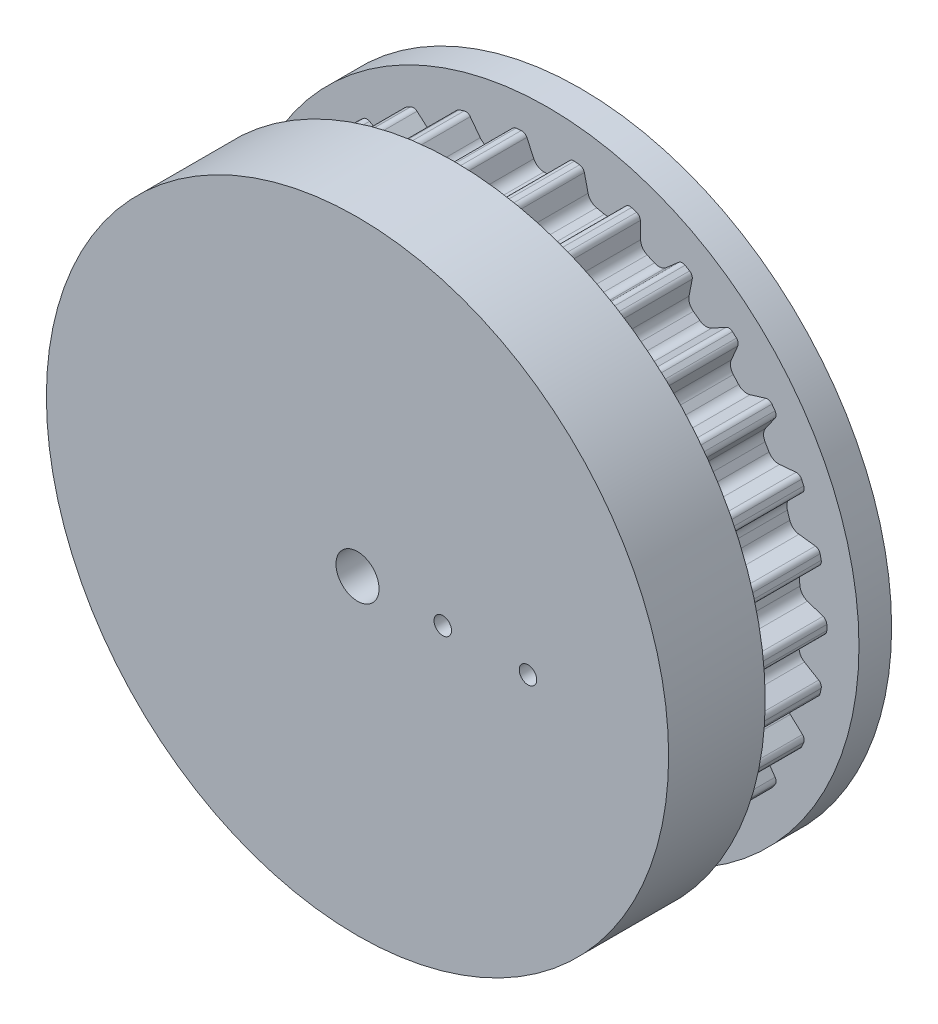
SolidWorks part; units mm, degrees
ref_plane "Front Plane" through (0, 0, 0) normal (0, 0, 1) x (1, 0, 0)
ref_plane "Top Plane" through (0, 0, 0) normal (0, 1, 0) x (1, 0, 0)
ref_plane "Right Plane" through (0, 0, 0) normal (1, 0, 0) x (0, 0, -1)
sketch "Sketch1" plane through (0, 0, 0) normal (0, 0, 1) x (1, 0, 0)
  line L0 (-5.3109, 65.2292) -> (-2.5867, 59.3872)
  line L1 (-2.5867, 59.3872) -> (2.5867, 59.3872)
  line L2 (2.5867, 59.3872) -> (5.3109, 65.2292)
  line L3 (-5.3109, 65.2292) -> (5.3109, 65.2292)
  line L4 (0, 0) -> (0, 59.3872) construction
  line L5 (0, 59.3872) -> (0, 66.84) construction
  circle A0 centre (0, 0) radius 66.84 construction
  circle A1 centre (0, 0) radius 65.445 construction
  circle A2 centre (0, 0) radius 65.445 construction
  circle A3 centre (0, 0) radius 73
  circle A4 centre (0, 0) radius 55.5
  circle A5 centre (0, 0) radius 20 construction
  point P6 (0, 65.2292)
  point P11 (0, 66.84)
  point P13 (0, 65.445)
  point P14 (0, 65.445)
  point P21 (13.5619, 63.8037)
  point P22 (26.5311, 59.5898)
  point P23 (38.3407, 52.7715)
  point P24 (48.4747, 43.6468)
  point P25 (56.4901, 32.6146)
  point P26 (62.0366, 20.1569)
  point P27 (64.8718, 6.8183)
  point P28 (64.8718, -6.8183)
  point P29 (62.0366, -20.1569)
  point P30 (56.4901, -32.6146)
  point P31 (48.4747, -43.6468)
  point P32 (38.3407, -52.7715)
  point P33 (26.5311, -59.5898)
  point P34 (13.5619, -63.8037)
  point P35 (0, -65.2292)
  point P36 (-13.5619, -63.8037)
  point P37 (-26.5311, -59.5898)
  point P38 (-38.3407, -52.7715)
  point P39 (-48.4747, -43.6468)
  point P40 (-56.4901, -32.6146)
  point P41 (-62.0366, -20.1569)
  point P42 (-64.8718, -6.8183)
  point P43 (-64.8718, 6.8183)
  point P44 (-62.0366, 20.1569)
  point P45 (-56.4901, 32.6146)
  point P46 (-48.4747, 43.6468)
  point P47 (-38.3407, 52.7715)
  point P48 (-26.5311, 59.5898)
  point P49 (-13.5619, 63.8037)
  point P52 (0, 0)
  dimension "Pitch Diameter" = 133.68
  dimension "Diameter" = 130.89
  dimension "OD" = 146
  dimension "Hub Diameter" = 111
  dimension "For Shaft Diameter" = 40
  dimension "b" = 50
  dimension "Tooth Width" = 10.6218
  dimension "ht" = 5.842
  dimension "Number of Teeth" = 30
sketch "Sketch2" plane through (0, 0, 0) normal (1, 0, 0) x (0, 0, -1)
  line L0 (29.335, 0) -> (-29.335, 0) construction
  line L3 (29.335, 20) -> (-29.335, 20)
  line L4 (-29.335, 20) -> (-29.335, 55.5)
  line L5 (29.335, 20) -> (29.335, 73)
  line L6 (29.335, 73) -> (21.675, 73)
  line L7 (21.675, 73) -> (21.675, 65.2292)
  line L8 (21.675, 65.2292) -> (-15.325, 65.2292)
  line L9 (-15.325, 65.2292) -> (-15.325, 73)
  line L10 (-15.325, 73) -> (-22.985, 73)
  line L11 (-29.335, 55.5) -> (-22.985, 55.5)
  line L12 (-22.985, 73) -> (-22.985, 55.5)
  line L13 (-22.985, 55.5) -> (0, 55.5) construction
  point P0 (0, 20)
  point P3 (0, 20)
  point P4 (0, 0)
  point P6 (0, 73)
  point P16 (21.675, 69.1146)
  dimension "Overall Width" = 58.67
  dimension "For Maximum Belt Width" = 37
  dimension "Outside Width" = 52.32
  dimension "Inside Width" = 37
sketch "Sketch10" plane through (0, 0, 0) normal (1, 0, 0) x (0, 0, -1)
  line L0 (-22.985, 20) -> (29.335, 20)
  line L1 (21.675, 65.445) -> (21.675, 73)
  line L2 (3.175, 0) -> (3.175, 65.445) construction
  line L3 (-22.985, 73) -> (-22.985, 55.5)
  line L4 (21.675, 73) -> (29.335, 73)
  line L5 (-15.325, 65.445) -> (-15.325, 73)
  line L6 (-15.325, 65.445) -> (21.675, 65.445)
  line L7 (-15.325, 73) -> (-22.985, 73)
  line L8 (-22.985, 55.5) -> (-29.335, 55.5)
  line L9 (29.335, 73) -> (29.335, 20)
  line L10 (-22.985, 0) -> (29.335, 0) construction
  line L11 (-29.335, 55.5) -> (-29.335, 20)
  line L12 (-29.335, 20) -> (-22.985, 20)
  line L13 (29.335, 20) -> (-29.335, 20) construction
  point P3 (-29.335, 0)
  point P9 (-15.325, -65.445)
  point P15 (0, 0)
  point P43 (-15.325, 65.445)
revolve "Revolve1" add sketch "Sketch10" angle 360 mid plane about L10
sketch "Sketch8" plane through (0, 0, 0) normal (0, 0, 1) x (1, 0, 0)
  circle A2 centre (0, 0) radius 20 construction
  circle A3 centre (0, 0) radius 20 construction
sketch "Sketch3" plane through (0, 0, 0) normal (0, 0, 1) x (1, 0, 0)
  line L0 (-2.5867, 59.3872) -> (2.5867, 59.3872) construction
  line L1 (2.5867, 59.3872) -> (5.3109, 65.2292) construction
  line L2 (-5.3109, 65.2292) -> (-2.5867, 59.3872) construction
  line L3 (-2.5867, 59.3872) -> (2.5867, 59.3872)
  line L4 (2.5867, 59.3872) -> (5.3109, 65.2292)
  line L5 (-5.3109, 65.2292) -> (-2.5867, 59.3872)
  circle A0 centre (0, 0) radius 65.445 construction
  arc A2 (5.3109, 65.2292) -> (-5.3109, 65.2292) centre (0, 0) ccw
extrude "Cut-Extrude1" cut sketch "Sketch3" against normal up to vertex (21.675 mm away) from vertex at 15.325 starting at point (0, 65.445, 15.325)
fillet "Fillet2" radius 1.2982 2 edges at (-5.3109, 65.2292, -3.175) (5.3109, 65.2292, -3.175)
fillet "Fillet1" radius 2.5964 2 edges at (-2.5867, 59.3872, -3.175) (2.5867, 59.3872, -3.175)
pattern_circular "CirPattern1" count 30 over 360 about axis through (0, 0, 0) along (0, 0, 1) of "Cut-Extrude1", "Fillet1", "Fillet2"
sketch "Sketch5" plane through (0, 0, -29.335) normal (0, 0, 1) x (1, 0, 0)
  circle A2 centre (0, 0) radius 22.54
  circle A4 centre (0, 0) radius 22.54
  dimension "D1" = 2.54
extrude "Cut-Extrude2" cut sketch "Sketch5" along normal blind 0.762
sketch "Sketch9" plane through (0, 0, 29.335) normal (0, 0, 1) x (1, 0, 0)
  circle A2 centre (0, 0) radius 22.54
  circle A3 centre (0, 0) radius 22.54
  dimension "D1" = 2.54
extrude "Cut-Extrude3" cut sketch "Sketch9" against normal blind 0.762
sketch "Sketch11" plane through (0, 0, 0) normal (0, 1, 0) x (1, 0, 0)
  line L0 (-55.5, -29.335) -> (55.5, -29.335) construction
  line L1 (-55.5, -22.985) -> (55.5, -22.985) construction
  line L2 (-55.5, -29.335) -> (55.5, -29.335)
  line L3 (-55.5, -22.985) -> (55.5, -22.985)
  line L4 (55.5, -29.335) -> (55.5, -22.985)
  line L5 (-55.5, -29.335) -> (-55.5, -22.985)
extrude "Cut-Extrude4" cut sketch "Sketch11" against normal mid plane 173
sketch "Sketch12" plane through (0, 0, 22.985) normal (0, 0, 1) x (1, 0, 0)
  circle A0 centre (0, 0) radius 20
extrude "Boss-Extrude1" add sketch "Sketch12" against normal up to surface (52.32 mm away) up to face at (22.54, 0, -29.335)
sketch "Sketch13" plane through (0, 0, 15.325) normal (0, 0, -1) x (-1, 0, 0)
  circle A1 centre (0, 0) radius 73
  circle A2 centre (0, 0) radius 73
  dimension "D1" = 0
extrude "Boss-Extrude2" add sketch "Sketch13" along normal blind 15
sketch "Sketch14" plane through (0, 0, 22.985) normal (0, 0, 1) x (1, 0, 0)
  line L0 (73, 0) -> (152.3118, 0) construction
  line L1 (72.3118, 10) -> (152.3118, 10)
  line L2 (72.3118, -10) -> (152.3118, -10)
  arc A0 (152.3118, -10) -> (152.3118, 10) centre (152.3118, 0) ccw
  circle A3 centre (0, 0) radius 73 construction
  arc A4 (72.3118, -10) -> (72.3118, 10) centre (0, 0) ccw
  point P1 (0, 0)
  dimension "D1" = 20
  dimension "D3" = 80
extrude "Boss-Extrude3" [suppressed] add sketch "Sketch14" against normal blind 5.715
hole_wizard "Hole1" [suppressed] positions "Sketch15" profile "Sketch16" legacy
sketch "Sketch15" [suppressed] plane through (0, 0, 22.985) normal (0, 0, 1) x (1, 0, 0)
  arc A0 (152.3118, -10) -> (152.3118, 10) centre (152.3118, 0) ccw construction
  point P0 (97.3118, 0)
  point P2 (152.3118, 0)
  dimension "D1" = 55
sketch "Sketch16" plane through (97.3118, 0, 22.985) normal (1, 0, 0) x (0, -1, 0)
  line L0 (0, 0) -> (0, 5.715)
  line L1 (0, 5.715) -> (2.55, 5.715)
  line L2 (2.55, 5.715) -> (2.55, 0)
  line L3 (2.55, 0) -> (0, 0)
  line L4 (0, 110) -> (0, -10) construction
  dimension "Diameter" = 5.1
  dimension "Depth" = 5.715
sketch "Sketch17" [suppressed] plane through (0, 0, 17.27) normal (0, 0, -1) x (-1, 0, 0)
  line L0 (-152.3118, -21) -> (-152.3118, -10)
  line L1 (-152.3118, -10) -> (-72.3118, -10)
  line L2 (-72.3118, -10) -> (-152.3118, -10) construction
  line L3 (-152.3118, -21) -> (-69.9142, -21)
  line L4 (0, 0) -> (-197.8604, 0) construction
  arc A0 (-72.3118, -10) -> (-72.3118, 10) centre (0, 0) ccw construction
  arc A1 (-72.3118, -10) -> (-69.9142, -21) centre (0, 0) ccw
  dimension "D1" = 21
extrude "Boss-Extrude4" [suppressed] add sketch "Sketch17" against normal up to surface (5.715 mm away)
sketch "Sketch18" [suppressed] plane through (0, 0, 17.27) normal (0, 0, -1) x (-1, 0, 0)
  line L0 (-152.3118, -21) -> (-69.9142, -21)
  line L1 (-152.3118, -21) -> (-152.3118, -26)
  line L2 (-152.3118, -26) -> (-68.2129, -26)
  arc A0 (-69.9142, -21) -> (-72.3118, 10) centre (0, 0) ccw construction
  arc A1 (-69.9142, -21) -> (-68.2129, -26) centre (0, 0) ccw
  dimension "D1" = 5
extrude "Boss-Extrude5" [suppressed] add sketch "Sketch18" against normal blind 20
mirror "Mirror2" [suppressed] about plane through (0, 0, 0) normal (0, 1, 0)
sketch "Sketch19" plane through (0, 0, -28.573) normal (0, 0, -1) x (-1, 0, 0)
  circle A0 centre (0, 0) radius 20 construction
  circle A1 centre (0, 0) radius 22.54 construction
  circle A2 centre (0, 0) radius 20
  circle A3 centre (0, 0) radius 22.54
extrude "Boss-Extrude6" add sketch "Sketch19" along normal up to surface (0.762 mm away) up to face at (22.54, 0, -29.335)
hole_wizard "Hole2" positions "Sketch20" profile "Sketch21" legacy
sketch "Sketch20" plane through (0, 0, 22.985) normal (0, 0, 1) x (1, 0, 0)
  point P0 (0, 0)
sketch "Sketch21" plane through (0, 0, 22.985) normal (1, 0, 0) x (0, -1, 0)
  line L0 (0, 0) -> (0, 52.32)
  line L1 (0, 52.32) -> (5.05, 52.32)
  line L2 (5.05, 52.32) -> (5.05, 0)
  line L3 (5.05, 0) -> (0, 0)
  line L4 (0, 110) -> (0, -10) construction
  dimension "Diameter" = 10.1
  dimension "Depth" = 52.32
sketch "Sketch22" plane through (0, 0, 22.985) normal (0, 0, 1) x (1, 0, 0)
  circle A0 centre (20, 0) radius 2.05
  circle A1 centre (40, 0) radius 2.05
  point P2 (45.6362, 0)
  dimension "D1" = 4.1
  dimension "D2" = 20
  dimension "D4" = 20
  dimension "D3" = 2
extrude "Cut-Extrude5" cut sketch "Sketch22" against normal up to surface (52.32 mm away)
equation "\"D1@Fillet1\"=\"D1@Fillet2\"*2"
equation "\"D1@Fillet2\"=\"ht@Sketch1\"/4.5"
equation "\"Tooth Width@Sketch1\" = \"ht@Sketch1\" / .55"
equation "\"D1@Sketch9\"=\"D1@Sketch5\""
equation "\"D1@Cut-Extrude3\"=\"D1@Cut-Extrude2\""
equation "\"Teeth@CirPattern1\"=\"Number of Teeth@Sketch1\""
